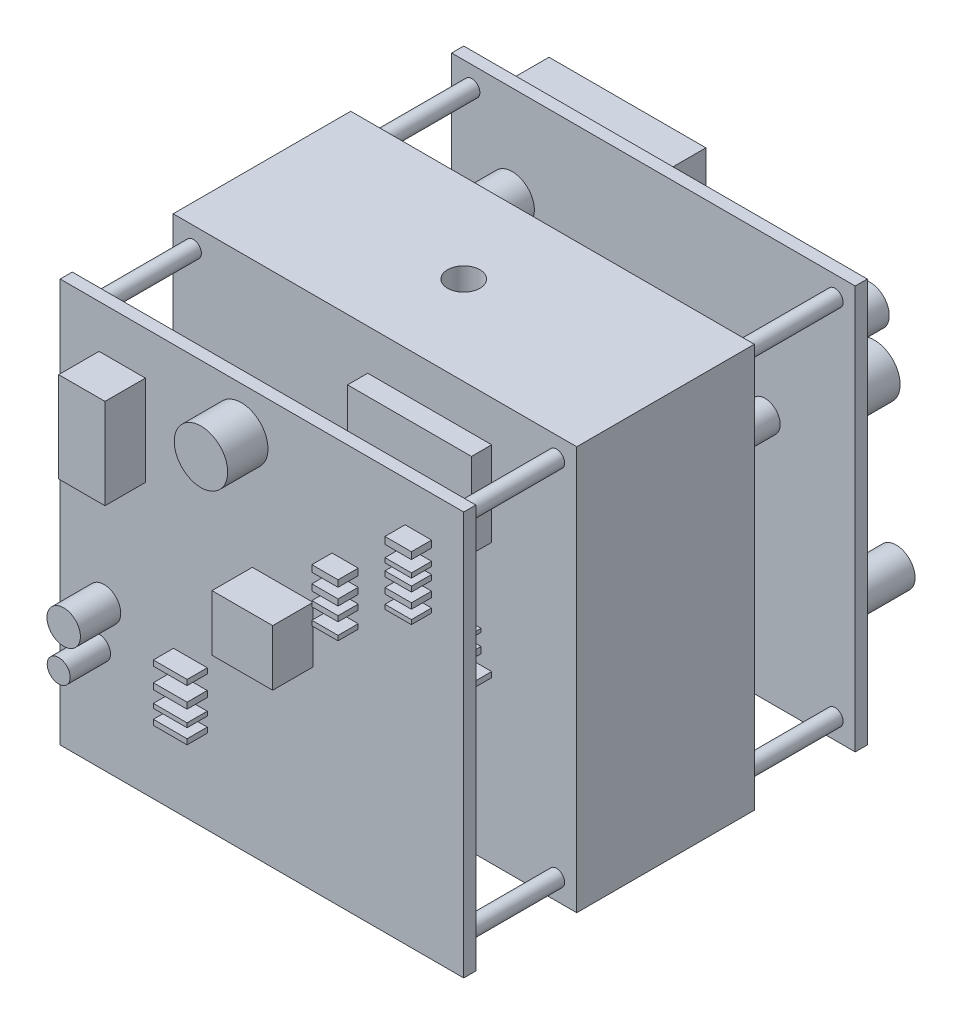
SolidWorks part; units mm, degrees
ref_plane "Alzado" through (0, 0, 0) normal (0, 0, 1) x (1, 0, 0)
ref_plane "Planta" through (0, 0, 0) normal (0, 1, 0) x (1, 0, 0)
ref_plane "Vista lateral" through (0, 0, 0) normal (1, 0, 0) x (0, 0, -1)
sketch "Croquis1" plane through (0, 0, 0) normal (0, 1, 0) x (1, 0, 0)
  line L1 (0, 0) -> (100, 0)
  line L2 (0, 0) -> (0, 100)
  line L3 (0, 100) -> (100, 100)
  line L4 (100, 0) -> (100, 100)
  dimension "D1" = 100
  dimension "D2" = 100
extrude "Saliente-Extruir1" add sketch "Croquis1" along normal blind 100
sketch "Croquis2" plane through (100, 0, 0) normal (1, 0, 0) x (0, 0, -1)
  line L0 (0, 100) -> (100, 100) construction
  line L1 (3, 100) -> (28, 100)
  line L2 (3, 100) -> (3, 0)
  line L3 (3, 0) -> (28, 0)
  line L4 (28, 100) -> (28, 0)
  line L5 (0, 0) -> (100, 0) construction
  line L6 (100, 100) -> (100, 0) construction
  line L7 (97, 100) -> (72, 100)
  line L8 (97, 100) -> (97, 0)
  line L9 (97, 0) -> (72, 0)
  line L10 (72, 100) -> (72, 0)
  line L11 (0, 100) -> (0, 0) construction
  dimension "D1" = 3
  dimension "D2" = 3
  dimension "D3" = 25
  dimension "D4" = 25
extrude "Cortar-Extruir1" cut sketch "Croquis2" against normal blind 100
sketch "Croquis3" plane through (0, 100, 0) normal (0, 1, 0) x (1, 0, 0)
  circle A0 centre (50, 50) radius 4
extrude "Cortar-Extruir2" cut sketch "Croquis3" against normal blind 100
sketch "Croquis4" plane through (0, 0, -100) normal (0, 0, -1) x (-1, 0, 0)
  circle A0 centre (-95, 95) radius 2
  circle A1 centre (-95, 5.0341) radius 2
  circle A2 centre (-5, 95) radius 2
  circle A3 centre (-5, 5.0341) radius 2
extrude "Saliente-Extruir2" add sketch "Croquis4" against normal blind 100
sketch "Croquis5" plane through (0, 0, -100) normal (0, 0, -1) x (-1, 0, 0)
  line L1 (-9.6277, 7.5862) -> (-37.6427, 7.5862)
  line L2 (-9.6277, 7.5862) -> (-9.6277, 16.638)
  line L3 (-9.6277, 16.638) -> (-37.6427, 16.638)
  line L4 (-37.6427, 7.5862) -> (-37.6427, 16.638)
  line L5 (-54.0188, 7.5862) -> (-51.0643, 7.5862)
  line L6 (-54.0188, 7.5862) -> (-54.0188, 16.638)
  line L7 (-54.0188, 16.638) -> (-51.0643, 16.638)
  line L8 (-51.0643, 7.5862) -> (-51.0643, 16.638)
  line L9 (-57.8034, 7.5862) -> (-61.2, 7.5862)
  line L10 (-57.8034, 7.5862) -> (-57.8034, 16.638)
  line L11 (-57.8034, 16.638) -> (-61.2, 16.638)
  line L12 (-61.2, 7.5862) -> (-61.2, 16.638)
  line L13 (-72.6351, 7.5862) -> (-75.3405, 7.5862)
  line L14 (-72.6351, 7.5862) -> (-72.6351, 16.638)
  line L15 (-72.6351, 16.638) -> (-75.3405, 16.638)
  line L16 (-75.3405, 7.5862) -> (-75.3405, 16.638)
  line L17 (-64.1127, 43.1942) -> (-52.5416, 43.1942)
  line L18 (-64.1127, 43.1942) -> (-64.1127, 54.2921)
  line L19 (-64.1127, 54.2921) -> (-52.5416, 54.2921)
  line L20 (-52.5416, 43.1942) -> (-52.5416, 54.2921)
extrude "Saliente-Extruir3" add sketch "Croquis5" along normal blind 5
sketch "Croquis6" plane through (0, 0, -100) normal (0, 0, -1) x (-1, 0, 0)
  circle A0 centre (-13.6647, 30.6535) radius 3.8405
  circle A1 centre (-92.1488, 26.813) radius 4.6861
extrude "Saliente-Extruir4" add sketch "Croquis6" along normal blind 15
sketch "Croquis7" plane through (0, 0, -100) normal (0, 0, -1) x (-1, 0, 0)
  line L1 (-45.0015, 66.8051) -> (-6.1224, 66.8051)
  line L2 (-45.0015, 66.8051) -> (-45.0015, 93.1544)
  line L3 (-45.0015, 93.1544) -> (-6.1224, 93.1544)
  line L4 (-6.1224, 66.8051) -> (-6.1224, 93.1544)
extrude "Saliente-Extruir5" add sketch "Croquis7" along normal blind 15
sketch "Croquis9" plane through (0, 0, -100) normal (0, 0, -1) x (-1, 0, 0)
  circle A0 centre (-90.6609, 84.8742) radius 4.785
  circle A1 centre (-91.7636, 71.405) radius 6.3679
  circle A2 centre (-80.5142, 84.8742) radius 2.4669
extrude "Saliente-Extruir7" add sketch "Croquis9" along normal blind 10
sketch "Croquis10" plane through (0, 0, -72) normal (0, 0, -1) x (-1, 0, 0)
  line L1 (-30.0148, 77.8571) -> (-62.556, 77.8571)
  line L2 (-30.0148, 77.8571) -> (-30.0148, 70.0466)
  line L3 (-30.0148, 70.0466) -> (-62.556, 70.0466)
  line L4 (-62.556, 77.8571) -> (-62.556, 70.0466)
  line L5 (-23.3053, 33.196) -> (-74.827, 33.196)
  line L6 (-23.3053, 33.196) -> (-23.3053, 56.7675)
  line L7 (-23.3053, 56.7675) -> (-74.827, 56.7675)
  line L8 (-74.827, 33.196) -> (-74.827, 56.7675)
  circle A0 centre (-82.0519, 25.2315) radius 5.7931
  circle A1 centre (-14.9828, 87.0887) radius 2.3181
  circle A2 centre (-30.0148, 91.5759) radius 5.4871
  circle A3 centre (-92.6484, 75.9654) radius 3.7633
extrude "Saliente-Extruir8" add sketch "Croquis10" along normal blind 10
sketch "Croquis11" plane through (0, 0, 0) normal (0, 0, 1) x (1, 0, 0)
  line L1 (9.6323, 89.2901) -> (21.1093, 89.2901)
  line L2 (9.6323, 89.2901) -> (9.6323, 66.8964)
  line L3 (9.6323, 66.8964) -> (21.1093, 66.8964)
  line L4 (21.1093, 89.2901) -> (21.1093, 66.8964)
  line L5 (47.6241, 61.9453) -> (62.655, 61.9453)
  line L6 (47.6241, 61.9453) -> (47.6241, 48.077)
  line L7 (47.6241, 48.077) -> (62.655, 48.077)
  line L8 (62.655, 61.9453) -> (62.655, 48.077)
  circle A0 centre (44.8863, 89.2901) radius 6.6186
  circle A1 centre (10.8696, 35.7473) radius 4.1396
  circle A2 centre (9.6323, 25.7544) radius 2.8445
extrude "Saliente-Extruir9" add sketch "Croquis11" along normal blind 10
sketch "Croquis12" plane through (0, 0, 0) normal (0, 0, 1) x (1, 0, 0)
  line L1 (28.087, 22.0626) -> (36.4463, 22.0626)
  line L2 (28.087, 22.0626) -> (28.087, 20.7533)
  line L3 (28.087, 20.7533) -> (36.4463, 20.7533)
  line L4 (36.4463, 22.0626) -> (36.4463, 20.7533)
  line L5 (28.087, 25.4815) -> (36.4463, 25.4815)
  line L6 (28.087, 25.4815) -> (28.087, 24.4144)
  line L7 (28.087, 24.4144) -> (36.4463, 24.4144)
  line L8 (36.4463, 25.4815) -> (36.4463, 24.4144)
  line L9 (28.087, 29.9161) -> (36.4463, 29.9161)
  line L10 (28.087, 29.9161) -> (28.087, 28.4092)
  line L11 (28.087, 28.4092) -> (36.4463, 28.4092)
  line L12 (36.4463, 29.9161) -> (36.4463, 28.4092)
  line L13 (28.087, 34.7962) -> (36.4463, 34.7962)
  line L14 (28.087, 34.7962) -> (28.087, 33.4596)
  line L15 (28.087, 33.4596) -> (36.4463, 33.4596)
  line L16 (36.4463, 34.7962) -> (36.4463, 33.4596)
extrude "Saliente-Extruir12" add sketch "Croquis12" along normal blind 5
sketch "Croquis13" plane through (0, 0, 0) normal (0, 0, 1) x (1, 0, 0)
  line L1 (92.0353, 88.2898) -> (85.4733, 88.2898)
  line L2 (92.0353, 88.2898) -> (92.0353, 89.9952)
  line L3 (92.0353, 89.9952) -> (85.4733, 89.9952)
  line L4 (85.4733, 88.2898) -> (85.4733, 89.9952)
  line L5 (92.0353, 85.4464) -> (85.4733, 85.4464)
  line L6 (92.0353, 85.4464) -> (92.0353, 84.3159)
  line L7 (92.0353, 84.3159) -> (85.4733, 84.3159)
  line L8 (85.4733, 85.4464) -> (85.4733, 84.3159)
  line L9 (92.0353, 82.6105) -> (85.4733, 82.6105)
  line L10 (92.0353, 82.6105) -> (92.0353, 81.323)
  line L11 (92.0353, 81.323) -> (85.4733, 81.323)
  line L12 (85.4733, 82.6105) -> (85.4733, 81.323)
  line L13 (92.0353, 79.0403) -> (85.4733, 79.0403)
  line L14 (92.0353, 79.0403) -> (92.0353, 77.6389)
  line L15 (92.0353, 77.6389) -> (85.4733, 77.6389)
  line L16 (85.4733, 79.0403) -> (85.4733, 77.6389)
  line L17 (92.0353, 75.4272) -> (85.4733, 75.4272)
  line L18 (92.0353, 75.4272) -> (92.0353, 74.3397)
  line L19 (92.0353, 74.3397) -> (85.4733, 74.3397)
  line L20 (85.4733, 75.4272) -> (85.4733, 74.3397)
  line L21 (73.8541, 74.8835) -> (67.3666, 74.8835)
  line L22 (73.8541, 74.8835) -> (73.8541, 73.2573)
  line L23 (73.8541, 73.2573) -> (67.3666, 73.2573)
  line L24 (67.3666, 74.8835) -> (67.3666, 73.2573)
  line L25 (73.8541, 70.7747) -> (67.3666, 70.7747)
  line L26 (73.8541, 70.7747) -> (73.8541, 69.2314)
  line L27 (73.8541, 69.2314) -> (67.3666, 69.2314)
  line L28 (67.3666, 70.7747) -> (67.3666, 69.2314)
  line L29 (73.8541, 67.1766) -> (67.3666, 67.1766)
  line L30 (73.8541, 67.1766) -> (73.8541, 65.8537)
  line L31 (73.8541, 65.8537) -> (67.3666, 65.8537)
  line L32 (67.3666, 67.1766) -> (67.3666, 65.8537)
  line L33 (73.8541, 62.9507) -> (67.3666, 62.9507)
  line L34 (73.8541, 62.9507) -> (73.8541, 61.7772)
  line L35 (73.8541, 61.7772) -> (67.3666, 61.7772)
  line L36 (67.3666, 62.9507) -> (67.3666, 61.7772)
extrude "Saliente-Extruir13" add sketch "Croquis13" along normal blind 5
sketch "Croquis14" plane through (0, 0, -28) normal (0, 0, 1) x (1, 0, 0)
  line L1 (48.2079, 89.8865) -> (78.9201, 89.8865)
  line L2 (48.2079, 89.8865) -> (48.2079, 68.9426)
  line L3 (48.2079, 68.9426) -> (78.9201, 68.9426)
  line L4 (78.9201, 89.8865) -> (78.9201, 68.9426)
  line L5 (54.1347, 57.0164) -> (73.5565, 57.0164)
  line L6 (54.1347, 57.0164) -> (54.1347, 55.8405)
  line L7 (54.1347, 55.8405) -> (73.5565, 55.8405)
  line L8 (73.5565, 57.0164) -> (73.5565, 55.8405)
  line L9 (54.1347, 53.3523) -> (74.9173, 53.3523)
  line L10 (54.1347, 53.3523) -> (54.1347, 52.0701)
  line L11 (54.1347, 52.0701) -> (74.9173, 52.0701)
  line L12 (74.9173, 53.3523) -> (74.9173, 52.0701)
  line L13 (55.7778, 49.1741) -> (76.2781, 49.1741)
  line L14 (55.7778, 49.1741) -> (55.7778, 48.2997)
  line L15 (55.7778, 48.2997) -> (76.2781, 48.2997)
  line L16 (76.2781, 49.1741) -> (76.2781, 48.2997)
  line L17 (57.7707, 45.2973) -> (76.2781, 45.2973)
  line L18 (57.7707, 45.2973) -> (57.7707, 43.7137)
  line L19 (57.7707, 43.7137) -> (76.2781, 43.7137)
  line L20 (76.2781, 45.2973) -> (76.2781, 43.7137)
  line L21 (57.7707, 41.2255) -> (78.9201, 41.2255)
  line L22 (57.7707, 41.2255) -> (57.7707, 39.9019)
  line L23 (57.7707, 39.9019) -> (78.9201, 39.9019)
  line L24 (78.9201, 41.2255) -> (78.9201, 39.9019)
extrude "Saliente-Extruir14" add sketch "Croquis14" along normal blind 5
